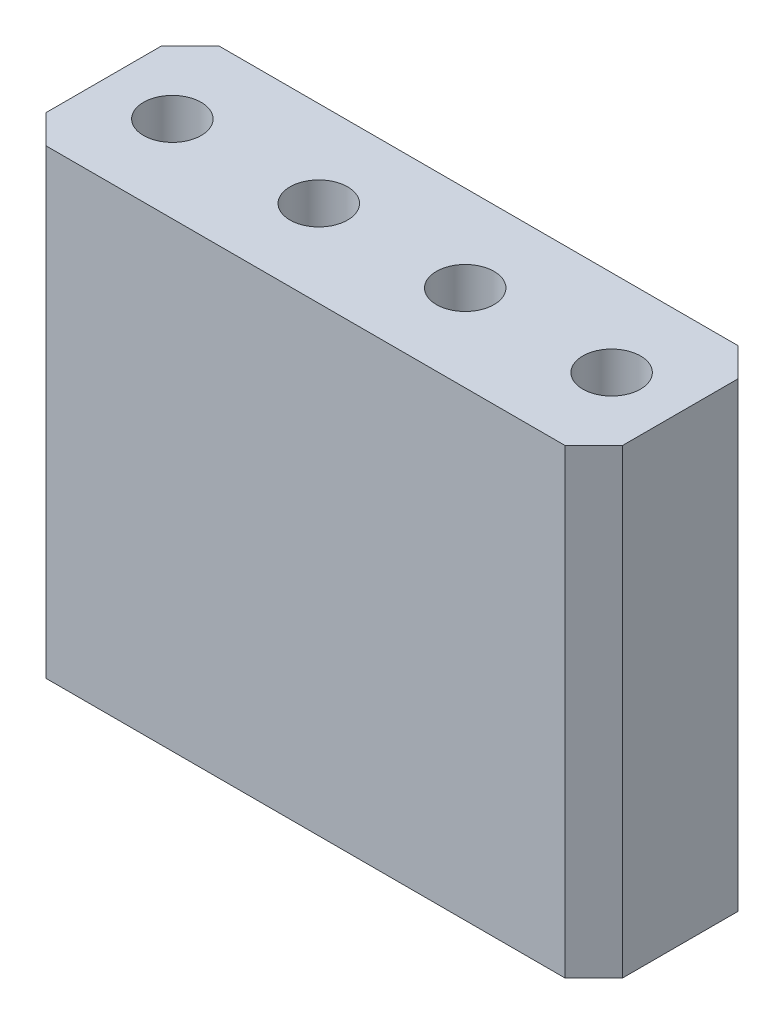
SolidWorks part; units mm, degrees
ref_plane "Спереди" through (0, 0, 0) normal (0, 0, 1) x (1, 0, 0)
ref_plane "Сверху" through (0, 0, 0) normal (0, 1, 0) x (1, 0, 0)
ref_plane "Справа" through (0, 0, 0) normal (1, 0, 0) x (0, 0, -1)
sketch "Эскиз1" plane through (0, 0, 0) normal (0, 1, 0) x (1, 0, 0)
  line L0 (-3.49, 0.32) -> (-3.49, -0.32)
  line L2 (-4.13, -0.32) -> (-4.13, 0.32)
  line L4 (4.13, -0.32) -> (4.13, 0.32)
  line L5 (-4.13, -0.32) -> (4.13, 0.32) construction
  line L6 (-4.13, 0.32) -> (4.13, -0.32) construction
  line L7 (-1.59, 0.32) -> (-1.59, -0.32)
  line L8 (-0.95, 0.32) -> (-0.95, -0.32)
  line L9 (0.95, 0.32) -> (0.95, -0.32)
  line L10 (1.59, 0.32) -> (1.59, -0.32)
  line L11 (3.49, 0.32) -> (3.49, -0.32)
  line L12 (-4.13, 0.32) -> (-3.49, 0.32)
  line L13 (-3.49, -0.32) -> (-4.13, -0.32)
  line L14 (-1.59, -0.32) -> (-0.95, -0.32)
  line L15 (-1.59, 0.32) -> (-0.95, 0.32)
  line L16 (0.95, 0.32) -> (1.59, 0.32)
  line L17 (1.59, -0.32) -> (0.95, -0.32)
  line L18 (3.49, 0.32) -> (4.13, 0.32)
  line L19 (4.13, -0.32) -> (3.49, -0.32)
  line L21 (-5, -1.5) -> (5, -1.5)
  line L22 (-5, -1.5) -> (-5, 1.5)
  line L23 (-5, 1.5) -> (5, 1.5)
  line L24 (5, -1.5) -> (5, 1.5)
  line L25 (-5, -1.5) -> (5, 1.5) construction
  line L26 (-5, 1.5) -> (5, -1.5) construction
  point P0 (0, 0)
  point P18 (0, 0)
  dimension "D1" = 8.26
  dimension "D2" = 0.64
  dimension "D3" = 0.64
  dimension "D4" = 1.9
  dimension "D5" = 0.64
  dimension "D6" = 1.9
  dimension "D7" = 0.64
  dimension "D8" = 1.9
  dimension "D9" = 10
  dimension "D10" = 3
  dimension "D11" = 1.18
  dimension "D12" = 0.87
extrude "Бобышка-Вытянуть1" add sketch "Эскиз1" along normal blind 6
sketch "Эскиз2" plane through (0, 6, 0) normal (0, 1, 0) x (1, 0, 0)
  line L0 (-4.13, 0.32) -> (-3.49, -0.32) construction
  line L1 (-5, -1.5) -> (5, -1.5)
  line L2 (-5, -1.5) -> (-5, 1.5)
  line L3 (-5, 1.5) -> (5, 1.5)
  line L4 (5, -1.5) -> (5, 1.5)
  line L5 (-5, -1.5) -> (5, 1.5) construction
  line L6 (-5, 1.5) -> (5, -1.5) construction
  line L7 (-1.59, 0.32) -> (-0.95, -0.32) construction
  line L8 (0.95, 0.32) -> (1.59, -0.32) construction
  line L9 (3.49, 0.32) -> (4.13, -0.32) construction
  circle A0 centre (-3.81, 0) radius 0.5
  circle A1 centre (-1.27, 0) radius 0.5
  circle A2 centre (1.27, 0) radius 0.5
  circle A3 centre (3.81, 0) radius 0.5
  point P0 (0, 0)
extrude "Бобышка-Вытянуть2" add sketch "Эскиз2" along normal blind 2
chamfer "Фаска1" distance 0.5 angle 45 6 edges at (-5, 4, 1.5) (0, 8, 1.5) (5, 4, 1.5) (0, 0, 1.5) (5, 4, -1.5) (-5, 4, -1.5)
